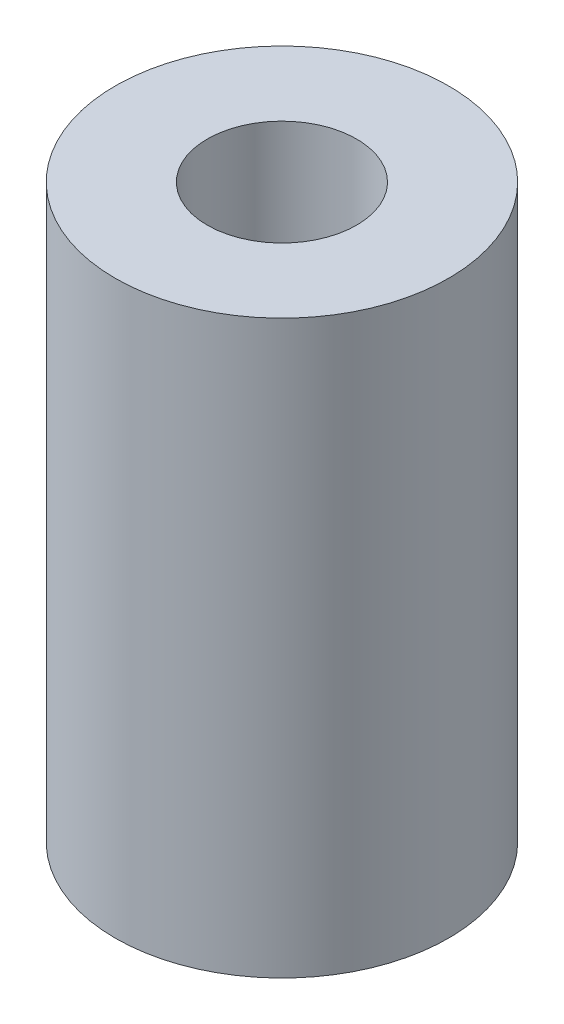
SolidWorks part; units mm, degrees
ref_plane "Front Plane" through (0, 0, 0) normal (0, 0, 1) x (1, 0, 0)
ref_plane "Top Plane" through (0, 0, 0) normal (0, 1, 0) x (1, 0, 0)
ref_plane "Right Plane" through (0, 0, 0) normal (1, 0, 0) x (0, 0, -1)
sketch "Sketch1" plane through (0, 0, 0) normal (0, 1, 0) x (1, 0, 0)
  circle A0 centre (0, 0) radius 3.45
  circle A1 centre (0, 0) radius 7.7
  dimension "D1" = 15.4
  dimension "D2" = 6.9
extrude "Boss-Extrude1" add sketch "Sketch1" along normal blind 26.4
